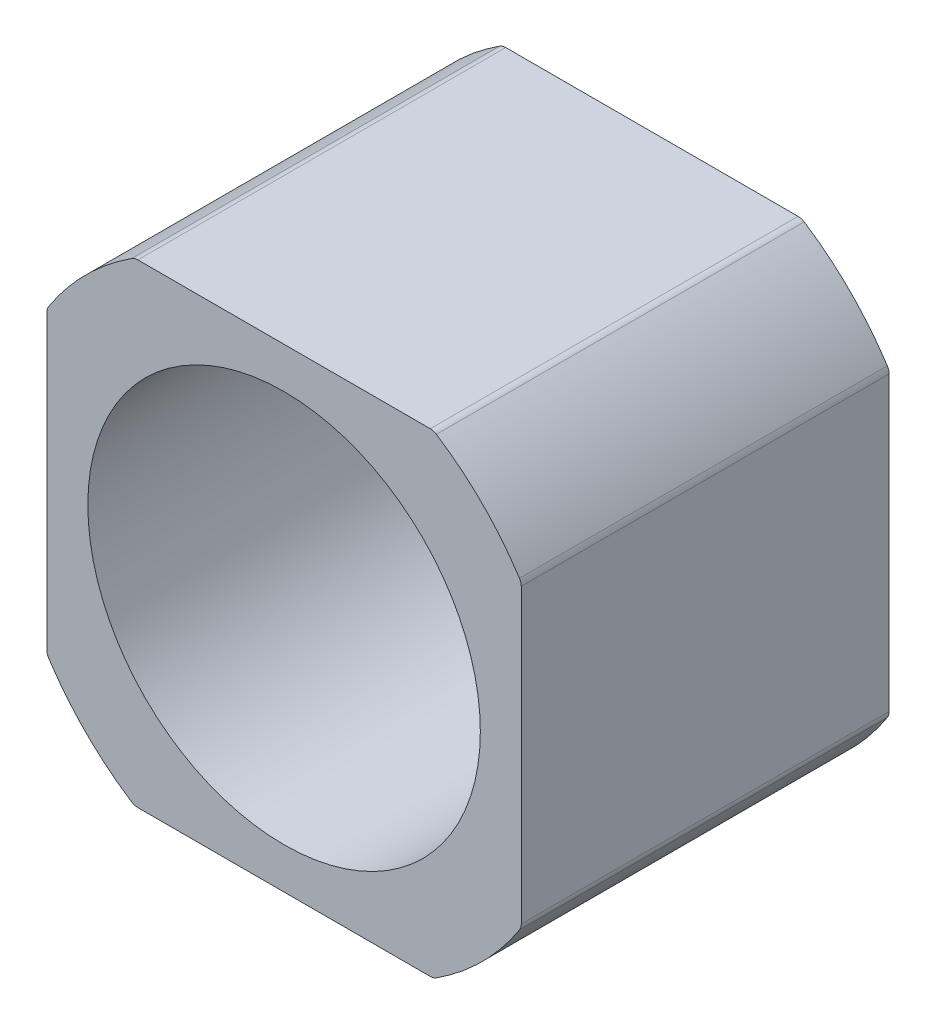
SolidWorks part; units mm, degrees
material "Acero aleado"
ref_plane "Alzado" through (0, 0, 0) normal (0, 0, 1) x (1, 0, 0)
ref_plane "Planta" through (0, 0, 0) normal (0, 1, 0) x (1, 0, 0)
ref_plane "Vista lateral" through (0, 0, 0) normal (1, 0, 0) x (0, 0, -1)
sketch "Croquis1" plane through (0, 0, 0) normal (0, 0, 1) x (1, 0, 0)
  line L0 (-21.15, 21.15) -> (21.15, 21.15)
  line L1 (-21.15, -21.15) -> (21.15, -21.15)
  line L2 (-21.15, 21.15) -> (-21.15, -21.15)
  line L4 (21.15, 21.15) -> (21.15, -21.15)
  line L5 (-21.15, 21.15) -> (21.15, -21.15) construction
  line L6 (-21.15, -21.15) -> (21.15, 21.15) construction
  point P0 (0, 0)
  dimension "D1" = 42.3
  dimension "D2" = 42.3
extrude "Saliente-Extruir1" add sketch "Croquis1" along normal blind 32.8
sketch "Sketch1" plane through (0, 0, 32.8) normal (0, 0, 1) x (1, 0, 0)
  circle A0 centre (0, 0) radius 25
  circle A1 centre (0, 0) radius 29.9106
  dimension "D1" = 50
extrude "Cut-Extrude1" cut sketch "Sketch1" against normal through all
fillet "Fillet1" radius 1 8 edges at (13.3296, 21.15, 16.4) (-13.3296, 21.15, 16.4) (-21.15, 13.3296, 16.4) (-21.15, -13.3296, 16.4) (-13.3296, -21.15, 16.4) (13.3296, -21.15, 16.4) (21.15, -13.3296, 16.4) (21.15, 13.3296, 16.4)
sketch "Sketch2" plane through (0, 0, 32.8) normal (0, 0, 1) x (1, 0, 0)
  circle A0 centre (0, 0) radius 17.5
  dimension "D1" = 35
extrude "Cut-Extrude2" cut sketch "Sketch2" against normal through all
